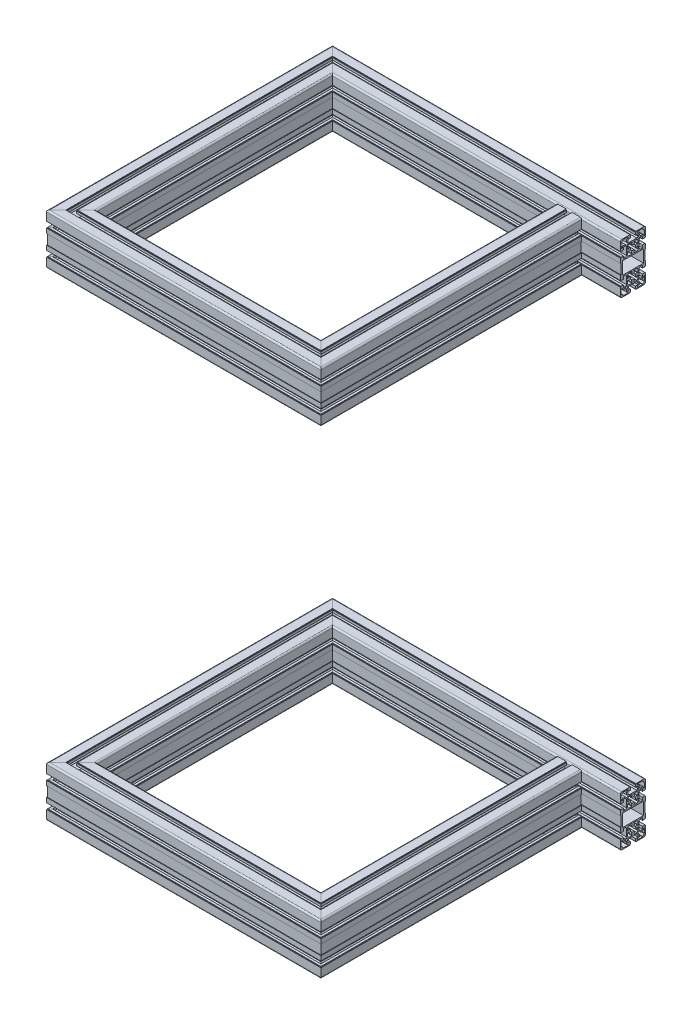
SolidWorks part; units mm, degrees
material "1060 Alloy"
material "1060 Alloy"
material "1060 Alloy"
material "1060 Alloy"
material "1060 Alloy"
ref_plane "Plano frontal" through (0, 0, 0) normal (0, 0, 1) x (1, 0, 0)
ref_plane "Plano superior" through (0, 0, 0) normal (0, 1, 0) x (1, 0, 0)
ref_plane "Plano direito" through (0, 0, 0) normal (1, 0, 0) x (0, 0, -1)
sketch3d "3DSketch1"
  line L0 (-22853.8611, 5527.6667, 40149.9002) -> (-23450.5611, 5527.6667, 40149.9002)
  line L2 (-23450.5611, 5527.6667, 40149.9002) -> (-23450.5611, 5527.6667, 40667.8588)
  line L3 (-23450.5611, 5527.6667, 40667.8588) -> (-22955.5611, 5527.6667, 40667.8588)
  line L4 (-22955.5611, 5527.6667, 40667.8588) -> (-22955.5611, 5527.6667, 40174.9002)
  line L7 (-23450.5611, 5527.6667, 40199.9002) -> (-22901.5611, 5527.6667, 40199.9002) construction
  line L8 (-22901.5611, 12327.8571, 40199.9002) -> (-22901.5611, -2672.1429, 40199.9002) construction
  line L9 (-23030.5611, 5527.6667, 40199.9002) -> (-23030.5611, 5527.6667, 40322.6002) construction
  line L10 (-23030.5611, 11528.5306, 40322.6002) -> (-23030.5611, -2137.13, 40322.6002) construction
  line L12 (-22850.5611, 5527.6667, 40199.9002) -> (-22850.5611, 5527.6667, 40762.6002) construction
  line L13 (-22850.5611, 4903.7221, 40762.6002) -> (-22850.5611, 6715.4106, 40762.6002) construction
  dimension "D1" = 50
  dimension "D2" = 420
  dimension "D3" = 75
  dimension "D5" = 25
ref_plane "Plane2" through (-23450.5611, 5527.6667, 40667.8588) normal (1, 0, 0) x (0, 0, -1)
other "Aluminium profile 50x100 50X100(1)"
ref_plane "Plane4" through (-23450.5611, 5527.6667, 40149.9002) normal (0, 0, 1) x (1, 0, 0)
sketch "Sketch1" plane through (-23450.5611, 5527.6667, 40149.9002) normal (0, 0, 1) x (1, 0, 0)
  line L0 (15.1906, 37.8447) -> (11.8847, 34.5389)
  line L1 (11.8847, 34.5389) -> (9.5389, 36.8847)
  line L2 (9.5389, 36.8847) -> (12.8447, 40.1906)
  line L3 (11.2262, 45.7) -> (9.5, 45.7)
  line L4 (9.5, 45.7) -> (9.5, 48.3)
  line L5 (9.5, 48.3) -> (19, 48.3)
  line L6 (19, 48.3) -> (19, 47.2697)
  line L7 (22.2697, 44) -> (23.3, 44)
  line L8 (23.3, 44) -> (23.3, 34.5)
  line L9 (23.3, 34.5) -> (20.7, 34.5)
  line L10 (20.7, 34.5) -> (20.7, 36.2262)
  line L11 (12.8447, -40.1906) -> (9.5389, -36.8847)
  line L12 (9.5389, -36.8847) -> (11.8847, -34.5389)
  line L13 (11.8847, -34.5389) -> (15.1906, -37.8447)
  line L14 (20.7, -36.2262) -> (20.7, -34.5)
  line L15 (20.7, -34.5) -> (23.3, -34.5)
  line L16 (23.3, -34.5) -> (23.3, -44)
  line L17 (23.3, -44) -> (22.2697, -44)
  line L18 (19, -47.2697) -> (19, -48.3)
  line L19 (19, -48.3) -> (9.5, -48.3)
  line L20 (9.5, -48.3) -> (9.5, -45.7)
  line L21 (9.5, -45.7) -> (11.2262, -45.7)
  line L22 (-19, 48.3) -> (-9.5, 48.3)
  line L23 (-9.5, 48.3) -> (-9.5, 45.7)
  line L24 (-9.5, 45.7) -> (-11.2262, 45.7)
  line L25 (-12.8447, 40.1906) -> (-9.5389, 36.8847)
  line L26 (-9.5389, 36.8847) -> (-11.8847, 34.5389)
  line L27 (-11.8847, 34.5389) -> (-15.1906, 37.8447)
  line L28 (-20.7, 36.2262) -> (-20.7, 34.5)
  line L29 (-20.7, 34.5) -> (-23.3, 34.5)
  line L30 (-23.3, 34.5) -> (-23.3, 44)
  line L31 (-23.3, 44) -> (-22.2697, 44)
  line L32 (-19, 47.2697) -> (-19, 48.3)
  line L33 (-23.3, -34.5) -> (-20.7, -34.5)
  line L34 (-20.7, -34.5) -> (-20.7, -36.2262)
  line L35 (-15.1906, -37.8447) -> (-11.8847, -34.5389)
  line L36 (-11.8847, -34.5389) -> (-9.5389, -36.8847)
  line L37 (-9.5389, -36.8847) -> (-12.8447, -40.1906)
  line L38 (-11.2262, -45.7) -> (-9.5, -45.7)
  line L39 (-9.5, -45.7) -> (-9.5, -48.3)
  line L40 (-9.5, -48.3) -> (-19, -48.3)
  line L41 (-19, -48.3) -> (-19, -47.2697)
  line L42 (-22.2697, -44) -> (-23.3, -44)
  line L43 (-23.3, -44) -> (-23.3, -34.5)
  line L44 (-10.3, -23) -> (-10.3, -16.9877)
  line L45 (-10.3, -16.9877) -> (-8.0123, -14.7)
  line L46 (-8.0123, -14.7) -> (-2, -14.7)
  line L47 (-2, -14.7) -> (-2, -16.5539)
  line L48 (-2, -16.5539) -> (-3.5923, -17.2964)
  line L49 (-3.5923, -17.2964) -> (-2.1131, -20.4685)
  line L50 (2.1131, -20.4685) -> (3.5923, -17.2964)
  line L51 (3.5923, -17.2964) -> (2, -16.5539)
  line L52 (2, -16.5539) -> (2, -14.7)
  line L53 (2, -14.7) -> (8.0123, -14.7)
  line L54 (8.0123, -14.7) -> (10.3, -16.9877)
  line L55 (10.3, -16.9877) -> (10.3, -23)
  line L56 (10.3, -23) -> (8.4461, -23)
  line L57 (8.4461, -23) -> (7.7036, -21.4077)
  line L58 (7.7036, -21.4077) -> (4.5315, -22.8869)
  line L59 (4.5315, -27.1131) -> (7.7036, -28.5923)
  line L60 (7.7036, -28.5923) -> (8.4461, -27)
  line L61 (8.4461, -27) -> (10.3, -27)
  line L62 (10.3, -27) -> (10.3, -33.0123)
  line L63 (10.3, -33.0123) -> (8.0123, -35.3)
  line L64 (8.0123, -35.3) -> (2, -35.3)
  line L65 (2, -35.3) -> (2, -33.4461)
  line L66 (2, -33.4461) -> (3.5923, -32.7036)
  line L67 (3.5923, -32.7036) -> (2.1131, -29.5315)
  line L68 (-2.1131, -29.5315) -> (-3.5923, -32.7036)
  line L69 (-3.5923, -32.7036) -> (-2, -33.4461)
  line L70 (-2, -33.4461) -> (-2, -35.3)
  line L71 (-2, -35.3) -> (-8.0123, -35.3)
  line L72 (-8.0123, -35.3) -> (-10.3, -33.0123)
  line L73 (-10.3, -33.0123) -> (-10.3, -27)
  line L74 (-10.3, -27) -> (-8.4461, -27)
  line L75 (-8.4461, -27) -> (-7.7036, -28.5923)
  line L76 (-7.7036, -28.5923) -> (-4.5315, -27.1131)
  line L77 (-4.5315, -22.8869) -> (-7.7036, -21.4077)
  line L78 (-7.7036, -21.4077) -> (-8.4461, -23)
  line L79 (-8.4461, -23) -> (-10.3, -23)
  line L80 (8.0123, 35.3) -> (10.3, 33.0123)
  line L81 (10.3, 33.0123) -> (10.3, 27)
  line L82 (10.3, 27) -> (8.4461, 27)
  line L83 (8.4461, 27) -> (7.7036, 28.5923)
  line L84 (7.7036, 28.5923) -> (4.5315, 27.1131)
  line L85 (4.5315, 22.8869) -> (7.7036, 21.4077)
  line L86 (7.7036, 21.4077) -> (8.4461, 23)
  line L87 (8.4461, 23) -> (10.3, 23)
  line L88 (10.3, 23) -> (10.3, 16.9877)
  line L89 (10.3, 16.9877) -> (8.0123, 14.7)
  line L90 (8.0123, 14.7) -> (2, 14.7)
  line L91 (2, 14.7) -> (2, 16.5539)
  line L92 (2, 16.5539) -> (3.5923, 17.2964)
  line L93 (3.5923, 17.2964) -> (2.1131, 20.4685)
  line L94 (-2.1131, 20.4685) -> (-3.5923, 17.2964)
  line L95 (-3.5923, 17.2964) -> (-2, 16.5539)
  line L96 (-2, 16.5539) -> (-2, 14.7)
  line L97 (-2, 14.7) -> (-8.0123, 14.7)
  line L98 (-8.0123, 14.7) -> (-10.3, 16.9877)
  line L99 (-10.3, 16.9877) -> (-10.3, 23)
  line L100 (-10.3, 23) -> (-8.4461, 23)
  line L101 (-8.4461, 23) -> (-7.7036, 21.4077)
  line L102 (-7.7036, 21.4077) -> (-4.5315, 22.8869)
  line L103 (-4.5315, 27.1131) -> (-7.7036, 28.5923)
  line L104 (-7.7036, 28.5923) -> (-8.4461, 27)
  line L105 (-8.4461, 27) -> (-10.3, 27)
  line L106 (-10.3, 27) -> (-10.3, 33.0123)
  line L107 (-10.3, 33.0123) -> (-8.0123, 35.3)
  line L108 (-8.0123, 35.3) -> (-2, 35.3)
  line L109 (-2, 35.3) -> (-2, 33.4461)
  line L110 (-2, 33.4461) -> (-3.5923, 32.7036)
  line L111 (-3.5923, 32.7036) -> (-2.1131, 29.5315)
  line L112 (2.1131, 29.5315) -> (3.5923, 32.7036)
  line L113 (3.5923, 32.7036) -> (2, 33.4461)
  line L114 (2, 33.4461) -> (2, 35.3)
  line L115 (2, 35.3) -> (8.0123, 35.3)
  line L116 (21, 12.45) -> (21, -12.45)
  line L117 (21, -12.45) -> (-21, -12.45)
  line L118 (-21, -12.45) -> (-21, 12.45)
  line L119 (-21, 12.45) -> (21, 12.45)
  line L120 (23.5, -30) -> (19, -30)
  line L121 (19, -30) -> (19, -35.05)
  line L122 (19, -35.05) -> (14.8, -35.05)
  line L123 (14.8, -35.05) -> (12.5, -32.75)
  line L124 (12.5, -32.75) -> (12.5, -17.25)
  line L125 (12.5, -17.25) -> (14.8, -14.95)
  line L126 (14.8, -14.95) -> (19, -14.95)
  line L127 (19, -14.95) -> (19, -20)
  line L128 (19, -20) -> (23.5, -20)
  line L129 (23.5, -20) -> (23.5, -19.2)
  line L130 (23.5, -19.2) -> (25, -19.2)
  line L131 (25, -19.2) -> (25, -10)
  line L132 (25, -10) -> (24, -10)
  line L133 (24, -10) -> (24, 10)
  line L134 (24, 10) -> (25, 10)
  line L135 (25, 10) -> (25, 19.2)
  line L136 (25, 19.2) -> (23.5, 19.2)
  line L137 (23.5, 19.2) -> (23.5, 20)
  line L138 (23.5, 20) -> (19, 20)
  line L139 (19, 20) -> (19, 14.95)
  line L140 (19, 14.95) -> (14.8, 14.95)
  line L141 (14.8, 14.95) -> (12.5, 17.25)
  line L142 (12.5, 17.25) -> (12.5, 32.75)
  line L143 (12.5, 32.75) -> (14.8, 35.05)
  line L144 (14.8, 35.05) -> (19, 35.05)
  line L145 (19, 35.05) -> (19, 30)
  line L146 (19, 30) -> (23.5, 30)
  line L147 (23.5, 30) -> (23.5, 30.8)
  line L148 (23.5, 30.8) -> (25, 30.8)
  line L149 (25, 30.8) -> (25, 47)
  line L150 (22, 50) -> (5.8, 50)
  line L151 (5.8, 50) -> (5.8, 48.5)
  line L152 (5.8, 48.5) -> (5, 48.5)
  line L153 (5, 48.5) -> (5, 44)
  line L154 (5, 44) -> (10.05, 44)
  line L155 (10.05, 44) -> (10.05, 39.8)
  line L156 (10.05, 39.8) -> (7.75, 37.5)
  line L157 (7.75, 37.5) -> (-7.75, 37.5)
  line L158 (-7.75, 37.5) -> (-10.05, 39.8)
  line L159 (-10.05, 39.8) -> (-10.05, 44)
  line L160 (-10.05, 44) -> (-5, 44)
  line L161 (-5, 44) -> (-5, 48.5)
  line L162 (-5, 48.5) -> (-5.8, 48.5)
  line L163 (-5.8, 48.5) -> (-5.8, 50)
  line L164 (-5.8, 50) -> (-22, 50)
  line L165 (-25, 47) -> (-25, 30.8)
  line L166 (-25, 30.8) -> (-23.5, 30.8)
  line L167 (-23.5, 30.8) -> (-23.5, 30)
  line L168 (-23.5, 30) -> (-19, 30)
  line L169 (-19, 30) -> (-19, 35.05)
  line L170 (-19, 35.05) -> (-14.8, 35.05)
  line L171 (-14.8, 35.05) -> (-12.5, 32.75)
  line L172 (-12.5, 32.75) -> (-12.5, 17.25)
  line L173 (-12.5, 17.25) -> (-14.8, 14.95)
  line L174 (-14.8, 14.95) -> (-19, 14.95)
  line L175 (-19, 14.95) -> (-19, 20)
  line L176 (-19, 20) -> (-23.5, 20)
  line L177 (-23.5, 20) -> (-23.5, 19.2)
  line L178 (-23.5, 19.2) -> (-25, 19.2)
  line L179 (-25, 19.2) -> (-25, 10)
  line L180 (-25, 10) -> (-24, 10)
  line L181 (-24, 10) -> (-24, -10)
  line L182 (-24, -10) -> (-25, -10)
  line L183 (-25, -10) -> (-25, -19.2)
  line L184 (-25, -19.2) -> (-23.5, -19.2)
  line L185 (-23.5, -19.2) -> (-23.5, -20)
  line L186 (-23.5, -20) -> (-19, -20)
  line L187 (-19, -20) -> (-19, -14.95)
  line L188 (-19, -14.95) -> (-14.8, -14.95)
  line L189 (-14.8, -14.95) -> (-12.5, -17.25)
  line L190 (-12.5, -17.25) -> (-12.5, -32.75)
  line L191 (-12.5, -32.75) -> (-14.8, -35.05)
  line L192 (-14.8, -35.05) -> (-19, -35.05)
  line L193 (-19, -35.05) -> (-19, -30)
  line L194 (-19, -30) -> (-23.5, -30)
  line L195 (-23.5, -30) -> (-23.5, -30.8)
  line L196 (-23.5, -30.8) -> (-25, -30.8)
  line L197 (-25, -30.8) -> (-25, -47)
  line L198 (-22, -50) -> (-5.8, -50)
  line L199 (-5.8, -50) -> (-5.8, -48.5)
  line L200 (-5.8, -48.5) -> (-5, -48.5)
  line L201 (-5, -48.5) -> (-5, -44)
  line L202 (-5, -44) -> (-10.05, -44)
  line L203 (-10.05, -44) -> (-10.05, -39.8)
  line L204 (-10.05, -39.8) -> (-7.75, -37.5)
  line L205 (-7.75, -37.5) -> (7.75, -37.5)
  line L206 (7.75, -37.5) -> (10.05, -39.8)
  line L207 (10.05, -39.8) -> (10.05, -44)
  line L208 (10.05, -44) -> (5, -44)
  line L209 (5, -44) -> (5, -48.5)
  line L210 (5, -48.5) -> (5.8, -48.5)
  line L211 (5.8, -48.5) -> (5.8, -50)
  line L212 (5.8, -50) -> (22, -50)
  line L213 (25, -47) -> (25, -30.8)
  line L214 (25, -30.8) -> (23.5, -30.8)
  line L215 (23.5, -30.8) -> (23.5, -30)
  arc A0 (15.5214, 37.9081) -> (15.1906, 37.8447) centre (15.4027, 37.6326) ccw
  arc A1 (12.8447, 40.1906) -> (12.9081, 40.5214) centre (12.6326, 40.4027) ccw
  arc A2 (12.9081, 40.5214) -> (12.674, 43.8077) centre (17.5, 42.5) cw
  arc A3 (12.674, 43.8077) -> (11.2262, 45.7) centre (11.2262, 44.2) ccw
  arc A4 (19, 47.2697) -> (22.2697, 44) centre (17.5, 42.5) cw
  arc A5 (20.7, 36.2262) -> (18.8077, 37.674) centre (19.2, 36.2262) ccw
  arc A6 (18.8077, 37.674) -> (15.5214, 37.9081) centre (17.5, 42.5) cw
  arc A7 (15.1906, -37.8447) -> (15.5214, -37.9081) centre (15.4027, -37.6326) ccw
  arc A8 (15.5214, -37.9081) -> (18.8077, -37.674) centre (17.5, -42.5) cw
  arc A9 (18.8077, -37.674) -> (20.7, -36.2262) centre (19.2, -36.2262) ccw
  arc A10 (22.2697, -44) -> (19, -47.2697) centre (17.5, -42.5) cw
  arc A11 (11.2262, -45.7) -> (12.674, -43.8077) centre (11.2262, -44.2) ccw
  arc A12 (12.674, -43.8077) -> (12.9081, -40.5214) centre (17.5, -42.5) cw
  arc A13 (12.9081, -40.5214) -> (12.8447, -40.1906) centre (12.6326, -40.4027) ccw
  arc A14 (-11.2262, 45.7) -> (-12.674, 43.8077) centre (-11.2262, 44.2) ccw
  arc A15 (-12.674, 43.8077) -> (-12.9081, 40.5214) centre (-17.5, 42.5) cw
  arc A16 (-12.9081, 40.5214) -> (-12.8447, 40.1906) centre (-12.6326, 40.4027) ccw
  arc A17 (-15.1906, 37.8447) -> (-15.5214, 37.9081) centre (-15.4027, 37.6326) ccw
  arc A18 (-15.5214, 37.9081) -> (-18.8077, 37.674) centre (-17.5, 42.5) cw
  arc A19 (-18.8077, 37.674) -> (-20.7, 36.2262) centre (-19.2, 36.2262) ccw
  arc A20 (-22.2697, 44) -> (-19, 47.2697) centre (-17.5, 42.5) cw
  arc A21 (-20.7, -36.2262) -> (-18.8077, -37.674) centre (-19.2, -36.2262) ccw
  arc A22 (-18.8077, -37.674) -> (-15.5214, -37.9081) centre (-17.5, -42.5) cw
  arc A23 (-15.5214, -37.9081) -> (-15.1906, -37.8447) centre (-15.4027, -37.6326) ccw
  arc A24 (-12.8447, -40.1906) -> (-12.9081, -40.5214) centre (-12.6326, -40.4027) ccw
  arc A25 (-12.9081, -40.5214) -> (-12.674, -43.8077) centre (-17.5, -42.5) cw
  arc A26 (-12.674, -43.8077) -> (-11.2262, -45.7) centre (-11.2262, -44.2) ccw
  arc A27 (-19, -47.2697) -> (-22.2697, -44) centre (-17.5, -42.5) cw
  arc A28 (-2.1131, -20.4685) -> (2.1131, -20.4685) centre (0, -25) cw
  arc A29 (4.5315, -22.8869) -> (4.5315, -27.1131) centre (0, -25) cw
  arc A30 (2.1131, -29.5315) -> (-2.1131, -29.5315) centre (0, -25) cw
  arc A31 (-4.5315, -27.1131) -> (-4.5315, -22.8869) centre (0, -25) cw
  arc A32 (4.5315, 27.1131) -> (4.5315, 22.8869) centre (0, 25) cw
  arc A33 (2.1131, 20.4685) -> (-2.1131, 20.4685) centre (0, 25) cw
  arc A34 (-4.5315, 22.8869) -> (-4.5315, 27.1131) centre (0, 25) cw
  arc A35 (-2.1131, 29.5315) -> (2.1131, 29.5315) centre (0, 25) cw
  arc A36 (25, 47) -> (22, 50) centre (22, 47) ccw
  arc A37 (-22, 50) -> (-25, 47) centre (-22, 47) ccw
  arc A38 (-25, -47) -> (-22, -50) centre (-22, -47) ccw
  arc A39 (22, -50) -> (25, -47) centre (22, -47) ccw
  point P282 (0, 0)
pattern_linear "LPattern1" count 2 spacing 950 along (0, 1, 0) of bodies 103 104 101 102
